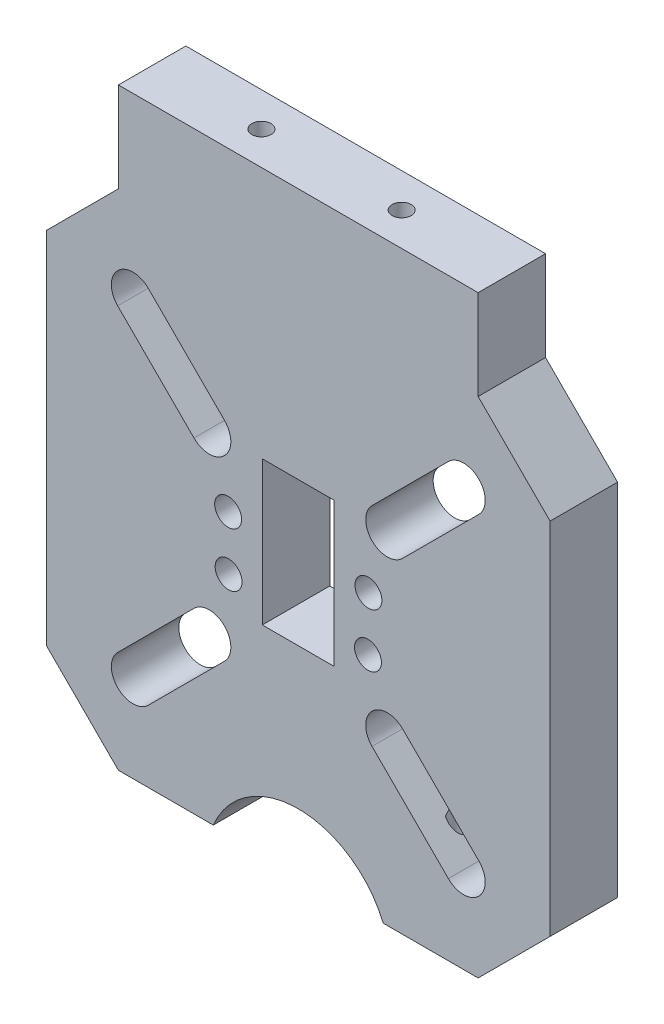
SolidWorks part; units mm, degrees
ref_plane "정면" through (0, 0, 0) normal (0, 0, 1) x (1, 0, 0)
ref_plane "윗면" through (0, 0, 0) normal (0, 1, 0) x (1, 0, 0)
ref_plane "우측면" through (0, 0, 0) normal (1, 0, 0) x (0, 0, -1)
sketch "Sketch1" plane through (0, 0, 0) normal (0, 0, 1) x (1, 0, 0)
  line L1 (0, 0) -> (-71.12, 0)
  line L2 (0, 0) -> (0, 71.12)
  line L3 (0, 71.12) -> (-71.12, 71.12)
  line L4 (-71.12, 0) -> (-71.12, 71.12)
  dimension "D1" = 71.12
  dimension "D2" = 71.12
extrude "Extrude1" add sketch "Sketch1" along normal blind 9.525
sketch "Sketch3" plane through (0, 0, 9.525) normal (0, 0, 1) x (1, 0, 0)
  line L0 (-71.12, 71.12) -> (0, 0)
  line L1 (0, 71.12) -> (-71.12, 0)
  line L2 (-58.9087, 58.9087) -> (-56.7534, 61.0639)
  line L3 (-56.7534, 61.0639) -> (-45.9771, 50.2876)
  line L4 (-45.9771, 50.2876) -> (-50.2876, 45.9771)
  line L5 (-50.2876, 45.9771) -> (-61.0639, 56.7534)
  line L6 (-61.0639, 56.7534) -> (-58.9087, 58.9087)
  circle A0 centre (-58.9087, 58.9087) radius 3.048
  circle A1 centre (-48.1324, 48.1324) radius 3.048
  dimension "D2" = 6.096
  dimension "D1" = 17.78
  dimension "D4" = 15.24
extrude "Cut-Extrude1" cut sketch "Sketch3" against normal through all contours A0 | L3 L4 L5 L6 L2 | A1
ref_plane "Plane1" through (-35.56, 0, 0) normal (1, 0, 0) x (0, 0, -1)
ref_plane "Plane2" through (0, 35.56, 0) normal (0, 1, 0) x (-1, 0, 0)
mirror "Mirror1" about plane through (0, 35.56, 0) normal (0, 1, 0) of "Cut-Extrude1"
mirror "Mirror2" about plane through (-35.56, 0, 0) normal (1, 0, 0) of "Cut-Extrude1"
mirror "Mirror3" about plane through (0, 35.56, 0) normal (0, 1, 0) of "Mirror2"
sketch "Sketch5" plane through (0, 0, 9.525) normal (0, 0, 1) x (1, 0, 0)
  line L0 (-71.12, 35.56) -> (0, 35.56)
  line L3 (-71.12, 71.12) -> (-71.12, 0) construction
  line L4 (0, 0) -> (0, 71.12) construction
  line L5 (-35.56, 35.56) -> (-35.56, 48.26)
  line L6 (-35.56, 48.26) -> (-40.64, 48.26)
  line L8 (-40.64, 48.26) -> (-30.48, 48.26)
  line L9 (-40.64, 48.26) -> (-40.64, 27.94)
  line L10 (-40.64, 27.94) -> (-30.48, 27.94)
  line L11 (-30.48, 48.26) -> (-30.48, 27.94)
  dimension "D1" = 12.7
  dimension "D2" = 5.08
  dimension "D3" = 10.16
  dimension "D4" = 20.32
extrude "Cut-Extrude4" cut sketch "Sketch5" against normal through all contours L9 L10 L11 L8
sketch "Sketch20" plane through (0, 0, 9.525) normal (0, 0, 1) x (1, 0, 0)
  line L1 (-35.56, 0) -> (-35.56, -5)
  line L2 (-71.12, 0) -> (0, 0) construction
  circle A0 centre (-35.56, -5) radius 13
  dimension "D1" = 5
  dimension "D2" = 26
extrude "Cut-Extrude5" cut sketch "Sketch20" against normal through all contours A0
chamfer "Chamfer1" distance 10.16 angle 45 1 edges at (-71.12, 71.12, 4.7625)
chamfer "Chamfer2" distance 10.16 angle 45 1 edges at (0, 71.12, 4.7625)
hole_wizard "#6 Clearance Hole1" positions "3DSketch9" profile "Sketch25" hole size "#6" standard "Ansi Inch"
sketch3d "3DSketch9"
  line L0 (-40.64, 48.26, 9.525) -> (-40.64, 27.94, 9.525) construction
  line L1 (-40.64, 27.94, 9.525) -> (-30.48, 27.94, 9.525) construction
  point P0 (-45.4025, 31.75, 9.525)
  point P2 (-45.466, 39.3697, 9.525)
  point P9 (-72.4079, 48.2314, 0)
  point P11 (16.2656, 58.2723, 0)
  dimension "D1" = 4.7625
  dimension "D2" = 4.826
  dimension "D3" = 7.62
  dimension "D4" = 3.81
sketch "Sketch25" plane through (-45.4025, 31.75, 9.525) normal (1, 0, 0) x (0, -1, 0)
  line L0 (0, 0) -> (0, 9.525)
  line L1 (0, 9.525) -> (1.8986, 9.525)
  line L2 (1.8986, 9.525) -> (1.8986, 0)
  line L5 (1.8986, 0) -> (0, 0)
  line L11 (0, -6.35) -> (0, 107.95) construction
  dimension "Thru Hole Dia." = 3.7973
  dimension "Thru Hole Depth" = 9.525
mirror "Mirror11" about plane through (-35.56, 0, 0) normal (1, 0, 0) of "#6 Clearance Hole1"
chamfer "Chamfer3" distance 10.16 angle 45 2 edges at (-71.12, 0, 4.7625) (0, 0, 4.7625)
sketch "Sketch26" plane through (0, 71.12, 0) normal (0, 1, 0) x (-1, 0, 0)
  line L1 (60.96, 0) -> (10.16, 0)
  line L2 (60.96, 0) -> (60.96, 9.525)
  line L3 (60.96, 9.525) -> (10.16, 9.525)
  line L4 (10.16, 0) -> (10.16, 9.525)
extrude "Extrude2" add sketch "Sketch26" along normal blind 12.7
hole_wizard "#6-32 Tapped Hole4" positions "3DSketch11" profile "Sketch28" tap size "#6-32" standard "Ansi Inch"
sketch3d "3DSketch11"
  line L0 (-60.96, 0, 9.525) -> (-60.96, 0, 0) construction
  line L2 (-60.96, 0, 0) -> (-47.56, 0, 0) construction
  line L4 (-23.56, 0, 0) -> (-10.16, 0, 0) construction
  point P0 (-53.34, 0, 4.7625)
  point P2 (-17.78, 0, 4.7625)
  dimension "D1" = 35.56
  dimension "D2" = 7.62
  dimension "D3" = 4.7625
  dimension "D4" = 4.7625
sketch "Sketch28" plane through (-53.34, 0, 4.7625) normal (1, 0, 0) x (0, 0, -1)
  line L0 (0, 0) -> (0, 14.7827)
  line L1 (0, 14.7827) -> (1.3525, 13.97)
  line L2 (1.3525, 13.97) -> (1.3525, 9.906)
  line L3 (1.3525, 9.906) -> (1.7526, 9.906)
  line L4 (1.7526, 9.906) -> (1.7526, 0)
  line L5 (1.7526, 0) -> (0, 0)
  line L10 (0, 14.7827) -> (-1.3526, 13.97) construction
  line L11 (0, -6.35) -> (0, 107.95) construction
  dimension "Tap Drill Dia." = 2.7051
  dimension "Tap Drill Depth" = 13.97
  dimension "Thread Major Dia." = 3.5052
  dimension "Thread Depth" = 9.906
  dimension "Drill Angle" = 118
sketch "Sketch29" plane through (0, 83.82, 0) normal (0, 1, 0) x (-1, 0, 0)
  line L0 (35.56, 0) -> (35.56, 9.525) construction
  line L1 (10.16, 0) -> (60.96, 0) construction
  line L2 (60.96, 9.525) -> (10.16, 9.525) construction
  point P6 (45.466, 4.826)
  point P7 (25.654, 4.826)
  dimension "D1" = 9.906
  dimension "D2" = 19.812
  dimension "D3" = 4.826
hole_wizard "#6-32 Tapped Hole5" positions "3DSketch12" profile "Sketch30" tap size "#6-32" standard "Ansi Inch"
sketch3d "3DSketch12"
  point P0 (-45.466, 83.82, 4.826)
  point P3 (-25.654, 83.82, 4.826)
sketch "Sketch30" plane through (-45.466, 83.82, 4.826) normal (1, 0, 0) x (0, 0, 1)
  line L0 (0, 0) -> (0, 14.7827)
  line L1 (0, 14.7827) -> (1.3525, 13.97)
  line L2 (1.3525, 13.97) -> (1.3525, 0)
  line L5 (1.3525, 0) -> (0, 0)
  line L10 (0, 14.7827) -> (-1.3525, 13.97) construction
  line L11 (0, -6.35) -> (0, 107.95) construction
  dimension "Tap Drill Dia." = 2.7051
  dimension "Tap Drill Depth" = 13.97
  dimension "Drill Angle" = 118
cosmetic thread "Hole Thread1" parameters "D1"=9.906, "D2"=3.5052
cosmetic thread "Hole Thread2" parameters "D1"=9.906, "D2"=3.5052
